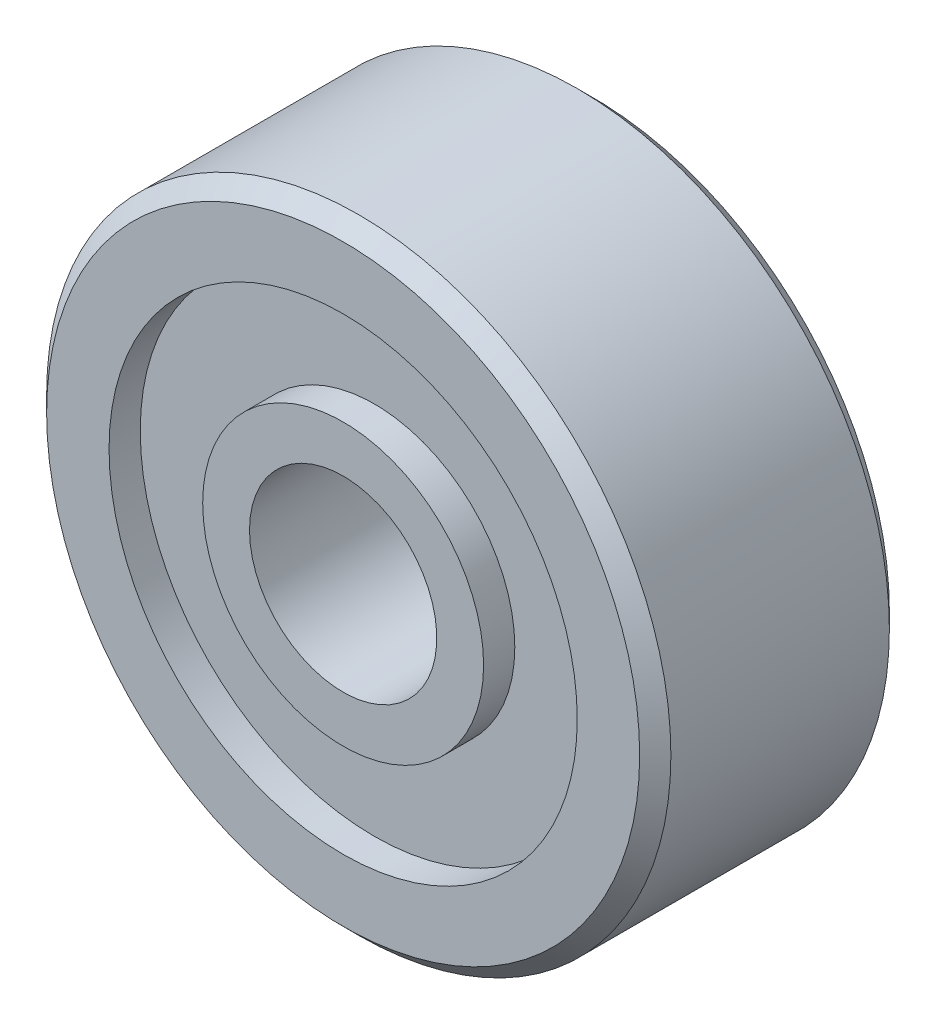
SolidWorks part; units mm, degrees
ref_plane "Front Plane" through (0, 0, 0) normal (0, 0, 1) x (1, 0, 0)
ref_plane "Top Plane" through (0, 0, 0) normal (0, 1, 0) x (1, 0, 0)
ref_plane "Right Plane" through (0, 0, 0) normal (1, 0, 0) x (0, 0, -1)
ref_plane "Plane1" through (0, 0, 0) normal (0, -1, 0) x (1, 0, 0)
sketch "Sketch1" plane through (0, 0, 0) normal (0, -1, 0) x (1, 0, 0)
  line L0 (6.5, 1.25) -> (6.25, 1.5)
  line L1 (6.25, 1.5) -> (5.25, 1.5)
  line L2 (5.25, 1.5) -> (5.25, 1)
  line L3 (5.25, 1) -> (3.75, 1)
  line L4 (3.75, 1) -> (3.75, 1.5)
  line L5 (3.75, 1.5) -> (3, 1.5)
  line L6 (3, 1.5) -> (3, -2.5)
  line L7 (3, -2.5) -> (3.75, -2.5)
  line L8 (3.75, -2.5) -> (3.75, -2)
  line L9 (3.75, -2) -> (5.25, -2)
  line L10 (5.25, -2) -> (5.25, -2.5)
  line L11 (5.25, -2.5) -> (6.25, -2.5)
  line L12 (6.25, -2.5) -> (6.5, -2.25)
  line L13 (6.5, -2.25) -> (6.5, 1.25)
  line L14 (1.5, 2.5) -> (1.5, -2.5) construction
  dimension "D1" = 3
  dimension "D2" = 10
  dimension "D3" = 4.5
  dimension "D4" = 4
  dimension "D5" = 0.5
  dimension "D6" = 45
  dimension "D7" = 0.5
  dimension "D8" = 45
revolve "Revolve1" add sketch "Sketch1" angle 360 about L14
